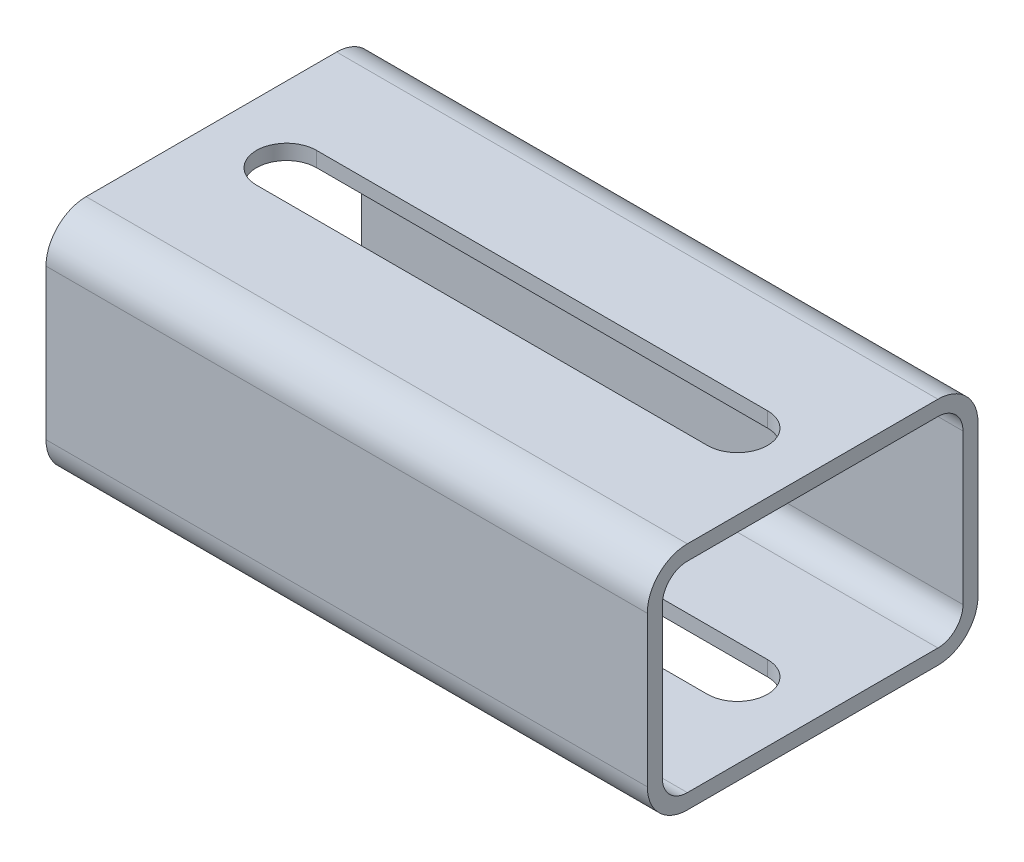
SolidWorks part; units mm, degrees
ref_plane "Front Plane" through (0, 0, 0) normal (0, 0, 1) x (1, 0, 0)
ref_plane "Top Plane" through (0, 0, 0) normal (0, 1, 0) x (1, 0, 0)
ref_plane "Right Plane" through (0, 0, 0) normal (1, 0, 0) x (0, 0, -1)
sketch "Sketch1" plane through (0, 0, 0) normal (1, 0, 0) x (0, 0, -1)
  line L1 (-25, -20) -> (25, -20)
  line L2 (-30, -15) -> (-30, 15)
  line L3 (-25, 20) -> (25, 20)
  line L4 (30, -15) -> (30, 15)
  line L5 (-30, -20) -> (30, 20) construction
  line L6 (-30, 20) -> (30, -20) construction
  arc A0 (25, 20) -> (30, 15) centre (25, 15) cw
  arc A1 (-25, -20) -> (-30, -15) centre (-25, -15) cw
  arc A2 (25, -20) -> (30, -15) centre (25, -15) ccw
  arc A3 (-25, 20) -> (-30, 15) centre (-25, 15) ccw
  point P0 (0, 0)
  dimension "D3" = 5
  dimension "width" = 60
  dimension "height" = 40
extrude "Extrude-Thin1" add sketch "Sketch1" along normal mid plane 120 thin
sketch "Sketch2" plane through (0, 23, 0) normal (0, 1, 0) x (1, 0, 0)
  line L0 (-45, 0) -> (45, 0) construction
  line L1 (-45, 6) -> (45, 6)
  line L2 (-45, -6) -> (45, -6)
  arc A0 (-45, 6) -> (-45, -6) centre (-45, 0) ccw
  arc A1 (45, -6) -> (45, 6) centre (45, 0) ccw
  point P2 (0, 0)
  dimension "D2" = 6
  dimension "D1" = 90
extrude "Cut-Extrude1" cut sketch "Sketch2" against normal through all
